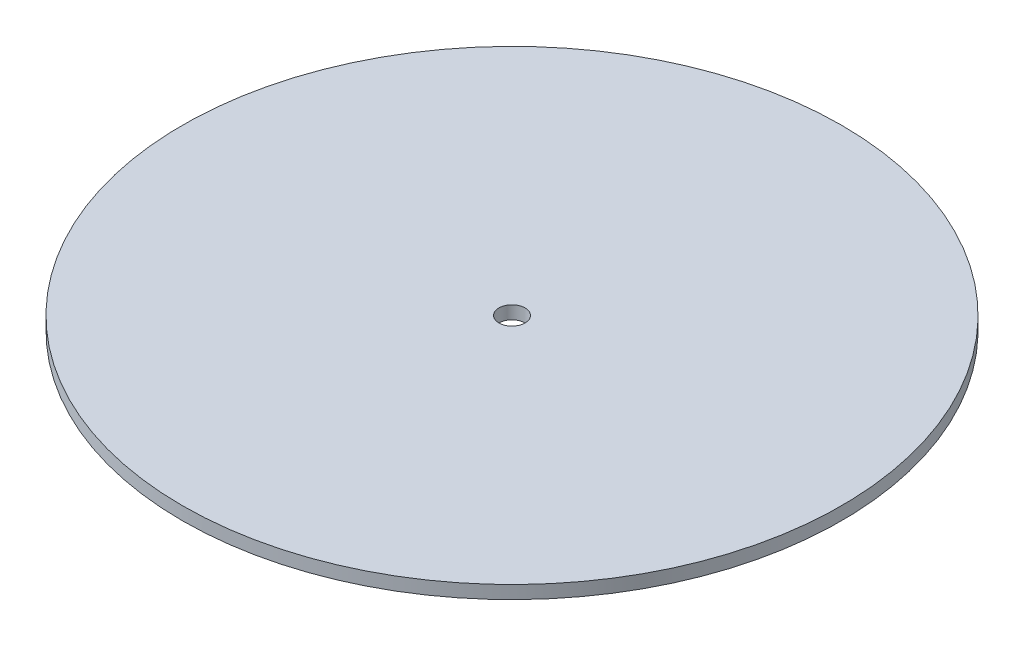
SolidWorks part; units mm, degrees
ref_plane "Front Plane" through (0, 0, 0) normal (0, 0, 1) x (1, 0, 0)
ref_plane "Top Plane" through (0, 0, 0) normal (0, 1, 0) x (1, 0, 0)
ref_plane "Right Plane" through (0, 0, 0) normal (1, 0, 0) x (0, 0, -1)
sketch "Sketch3" plane through (0, 0, 0) normal (0, 1, 0) x (1, 0, 0)
  circle A0 centre (0, 0) radius 126
extrude "Boss-Extrude1" add sketch "Sketch3" along normal blind 5
sketch "Sketch4" plane through (0, 5, 0) normal (0, 1, 0) x (1, 0, 0)
  circle A0 centre (0, 0) radius 5
extrude "Cut-Extrude1" cut sketch "Sketch4" against normal blind 5
